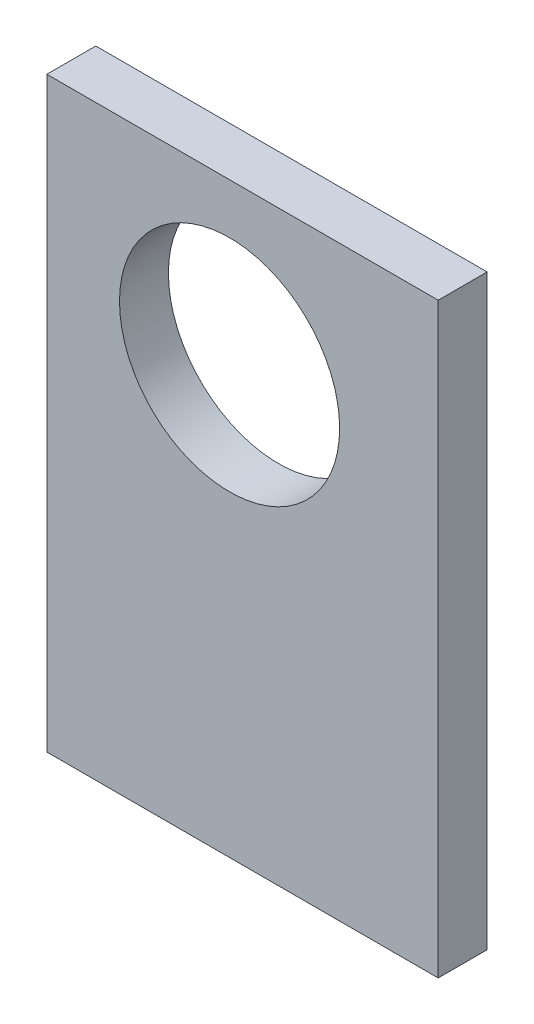
SolidWorks part; units mm, degrees
ref_plane "Front Plane" through (0, 0, 0) normal (0, 0, 1) x (1, 0, 0)
ref_plane "Top Plane" through (0, 0, 0) normal (0, 1, 0) x (1, 0, 0)
ref_plane "Right Plane" through (0, 0, 0) normal (1, 0, 0) x (0, 0, -1)
sketch "Sketch1" plane through (0, 0, 0) normal (0, 0, 1) x (1, 0, 0)
  line L1 (-51.1375, 48.606) -> (-0.3375, 48.606)
  line L2 (-51.1375, 48.606) -> (-51.1375, -27.594)
  line L3 (-51.1375, -27.594) -> (-0.3375, -27.594)
  line L4 (-0.3375, 48.606) -> (-0.3375, -27.594)
  dimension "D1" = 76.2
  dimension "D2" = 50.8
extrude "Boss-Extrude1" add sketch "Sketch1" along normal blind 6.35
sketch "Sketch2" plane through (0, 0, 6.35) normal (0, 0, 1) x (1, 0, 0)
  circle A0 centre (-27.4218, 27.8026) radius 14.2875
  dimension "D1" = 28.575
extrude "Cut-Extrude1" cut sketch "Sketch2" against normal blind 6.35
